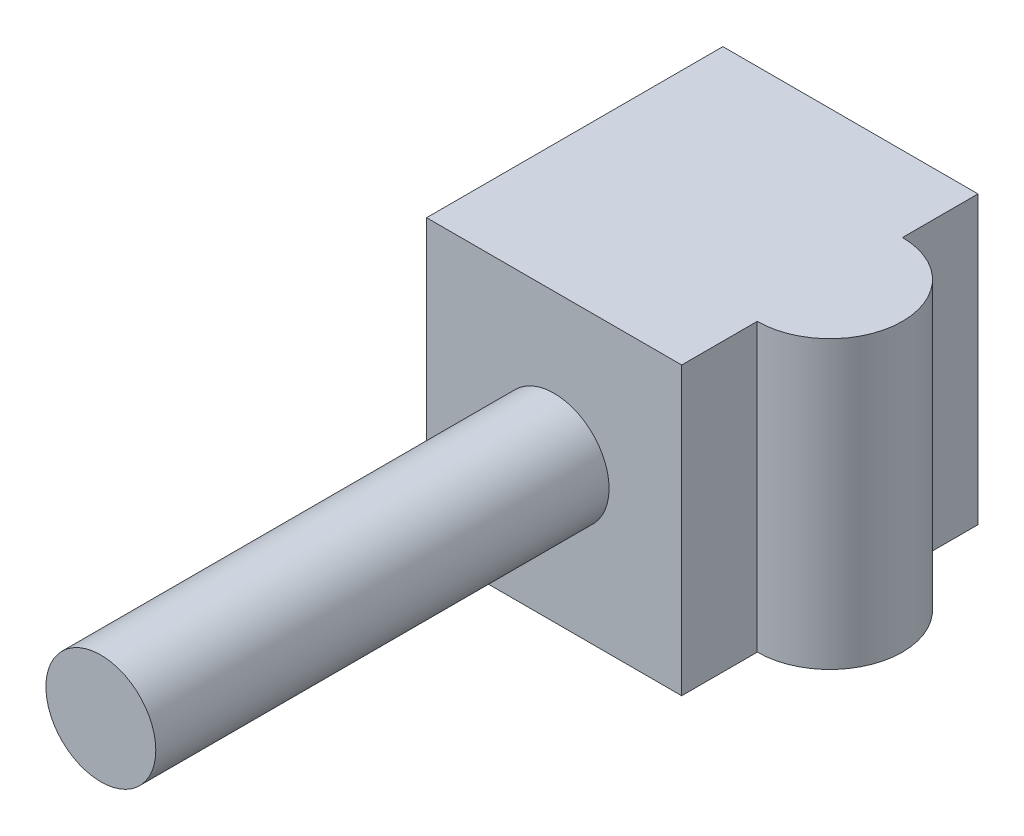
SolidWorks part; units mm, degrees
ref_plane "Plano frontal" through (0, 0, 0) normal (0, 0, 1) x (1, 0, 0)
ref_plane "Plano superior" through (0, 0, 0) normal (0, 1, 0) x (1, 0, 0)
ref_plane "Plano direito" through (0, 0, 0) normal (1, 0, 0) x (0, 0, -1)
sketch "Esboço1" plane through (0, 0, 0) normal (0, 0, 1) x (1, 0, 0)
  line L1 (-32.5, 36.5) -> (32.5, 36.5)
  line L2 (-32.5, 36.5) -> (-32.5, -36.5)
  line L3 (-32.5, -36.5) -> (32.5, -36.5)
  line L4 (32.5, 36.5) -> (32.5, -36.5)
  line L5 (-32.5, 36.5) -> (32.5, -36.5) construction
  line L6 (-32.5, -36.5) -> (32.5, 36.5) construction
  point P0 (0, 0)
  dimension "D1" = 65
  dimension "D2" = 73
extrude "Ressalto-extrusão1" add sketch "Esboço1" along normal mid plane 75.5
sketch "Esboço2" plane through (0, 0, -37.75) normal (0, 0, -1) x (-1, 0, 0)
  circle A0 centre (0, 0) radius 9
  dimension "D1" = 18
extrude "Corte-extrusão1" cut sketch "Esboço2" against normal blind 105.5
sketch "Esboço3" plane through (0, 0, 37.75) normal (0, 0, 1) x (1, 0, 0)
  circle A0 centre (0, 0) radius 14
  dimension "D1" = 28
extrude "Ressalto-extrusão2" add sketch "Esboço3" along normal blind 115.5
sketch "Esboço4" plane through (0, 36.5, 0) normal (0, 1, 0) x (1, 0, 0)
  line L0 (32.5, -37.75) -> (32.5, 37.75) construction
  circle A0 centre (32.5, 0) radius 18.5
  dimension "D1" = 37
extrude "Ressalto-extrusão3" add sketch "Esboço4" against normal blind 73
